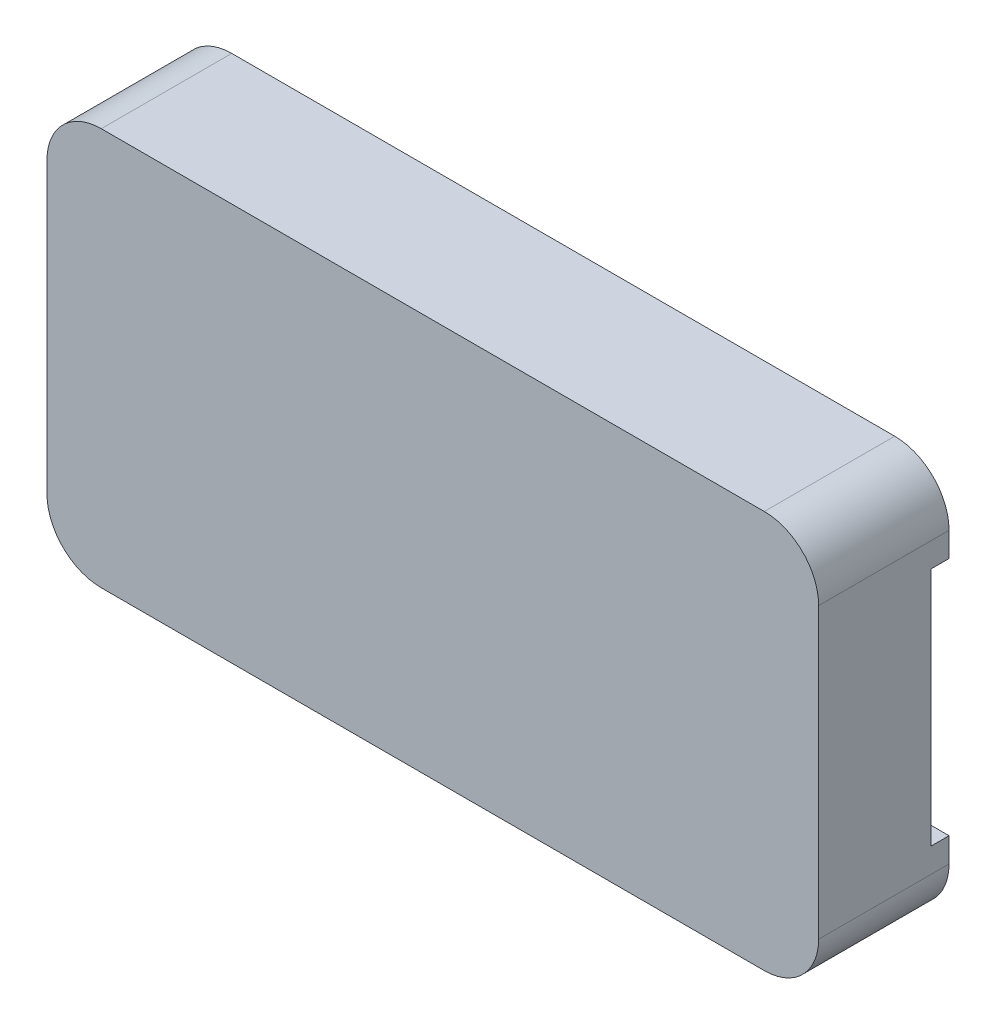
SolidWorks part; units mm, degrees
ref_plane "Plan de face" through (0, 0, 0) normal (0, 0, 1) x (1, 0, 0)
ref_plane "Plan de dessus" through (0, 0, 0) normal (0, 1, 0) x (1, 0, 0)
ref_plane "Plan de droite" through (0, 0, 0) normal (1, 0, 0) x (0, 0, -1)
sketch "Sketch2" plane through (0, 0, 0) normal (0, 0, 1) x (1, 0, 0)
  line L1 (21.3, -10.975) -> (-21.3, -10.975)
  line L2 (21.3, -10.975) -> (21.3, 10.975)
  line L3 (21.3, 10.975) -> (-21.3, 10.975)
  line L4 (-21.3, -10.975) -> (-21.3, 10.975)
  line L5 (21.3, -10.975) -> (-21.3, 10.975) construction
  line L6 (21.3, 10.975) -> (-21.3, -10.975) construction
  point P0 (0, 0)
  dimension "D1" = 42.6
  dimension "D2" = 21.95
extrude "Boss-Extrude1" add sketch "Sketch2" along normal blind 7.2
fillet "Fillet1" radius 3 4 edges at (-21.3, -10.975, 3.6) (21.3, -10.975, 3.6) (21.3, 10.975, 3.6) (-21.3, 10.975, 3.6)
sketch "Sketch3" plane through (0, 0, 0) normal (0, 0, -1) x (-1, 0, 0)
  line L0 (-21.3, 6.625) -> (-17.23, 6.625)
  line L1 (-21.3, -7.975) -> (-21.3, 7.975) construction
  line L2 (-17.23, 6.625) -> (-17.23, -6.625)
  line L3 (-17.23, -6.625) -> (-21.3, -6.625)
  line L4 (21.3, 7.975) -> (21.3, -7.975) construction
  line L5 (-18.3, 10.975) -> (18.3, 10.975) construction
  line L6 (18.3, -10.975) -> (-18.3, -10.975) construction
  line L7 (-21.3, 6.625) -> (-21.3, -6.625)
  dimension "D1" = 38.53
  dimension "D2" = 4.35
  dimension "D3" = 4.35
extrude "Cut-Extrude1" cut sketch "Sketch3" against normal blind 5.2
sketch "Sketch4" plane through (0, 0, 5.2) normal (0, 0, -1) x (-1, 0, 0)
  line L0 (-20.15, 4.925) -> (-20.15, -4.925)
  line L1 (-20.15, -4.925) -> (-18.4, -4.925)
  line L2 (-18.4, -4.925) -> (-18.4, -3.815)
  line L3 (-18.4, -3.815) -> (-19.11, -3.815)
  line L4 (-19.11, -3.815) -> (-19.11, -0.555)
  line L5 (-19.11, -0.555) -> (-18.4, -0.555)
  line L6 (-18.4, -0.555) -> (-18.4, 0.555)
  line L7 (-18.4, 0.555) -> (-19.11, 0.555)
  line L8 (-19.11, 0.555) -> (-19.11, 3.815)
  line L9 (-19.11, 3.815) -> (-18.4, 3.815)
  line L10 (-18.4, 3.815) -> (-18.4, 4.925)
  line L11 (-18.4, 4.925) -> (-20.15, 4.925)
  line L12 (21.3, 7.975) -> (21.3, -7.975) construction
  line L13 (-21.3, 6.625) -> (-21.3, -6.625) construction
  line L15 (18.3, -10.975) -> (-18.3, -10.975) construction
  point P16 (-20.15, 0)
  dimension "D1" = 41.45
  dimension "D2" = 2.9
  dimension "D3" = 15.9
  dimension "D4" = 1.04
  dimension "D5" = 1.11
extrude "Boss-Extrude2" add sketch "Sketch4" along normal blind 5.2
sketch "Sketch5" plane through (0, 0, 5.2) normal (0, 0, -1) x (-1, 0, 0)
  line L3 (-21.3, 6.625) -> (-21.3, -6.625)
  line L7 (-21.3, 6.625) -> (-19.9, 6.625)
  line L8 (-17.23, 6.625) -> (-21.3, 6.625) construction
  line L9 (-19.9, 6.625) -> (-19.9, 4.925)
  line L10 (-18.4, 4.925) -> (-20.15, 4.925) construction
  line L11 (-19.9, 4.925) -> (-20.15, 4.925)
  line L12 (-20.15, 4.925) -> (-20.15, -4.925)
  line L13 (-20.15, -4.925) -> (-19.9, -4.925)
  line L14 (-20.15, -4.925) -> (-18.4, -4.925) construction
  line L15 (-19.9, -4.925) -> (-19.9, -6.625)
  line L16 (-21.3, -6.625) -> (-17.23, -6.625) construction
  line L17 (-19.9, -6.625) -> (-21.3, -6.625)
  dimension "D1" = 0.25
  dimension "D2" = 0.25
extrude "Boss-Extrude3" add sketch "Sketch5" along normal blind 4.2
